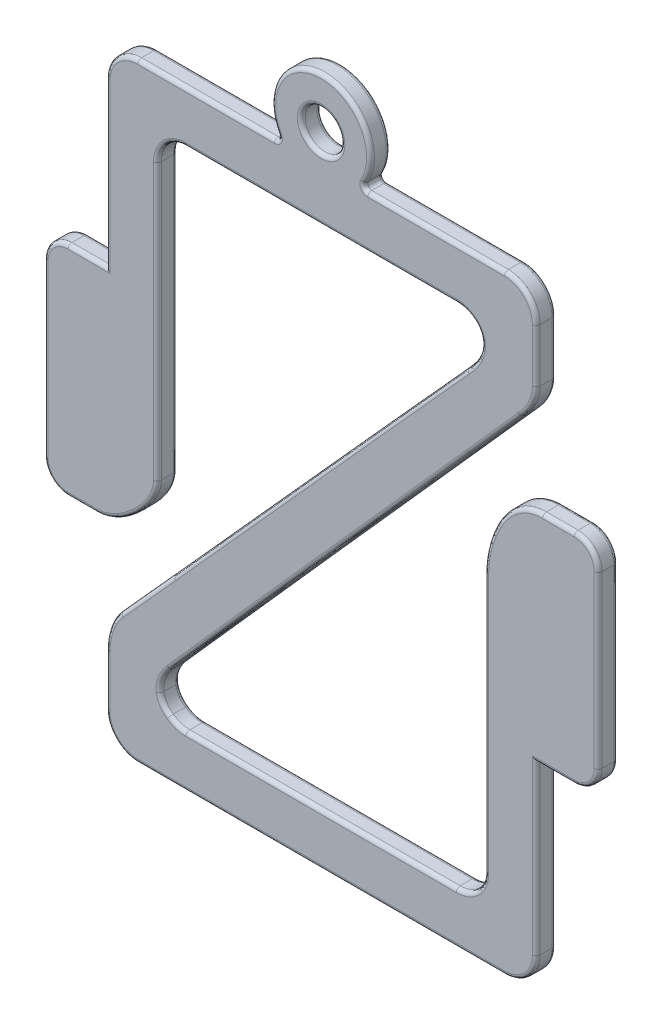
SolidWorks part; units mm, degrees
ref_plane "Front Plane" through (0, 0, 0) normal (0, 0, 1) x (1, 0, 0)
ref_plane "Top Plane" through (0, 0, 0) normal (0, 1, 0) x (1, 0, 0)
ref_plane "Right Plane" through (0, 0, 0) normal (1, 0, 0) x (0, 0, -1)
sketch "Model" plane through (0, 0, 0) normal (0, 0, 1) x (1, 0, 0)
  line L0 (214.5261, -387.7216) -> (400.0983, -387.7216)
  line L1 (416.1801, -371.6397) -> (416.1801, -286.4355)
  line L2 (416.1801, -286.4355) -> (435.3281, -286.4355)
  line L3 (447.4755, -274.288) -> (447.4755, -188.0817)
  line L4 (390.072, -215.7441) -> (390.072, -347.2106)
  line L5 (375.6692, -361.6134) -> (238.9382, -361.6134)
  line L6 (382.343, -168.4294) -> (408.5034, -139.0448)
  line L7 (416.1801, -122.3426) -> (416.1801, -95.415)
  line L8 (400.0983, -79.3331) -> (327.2017, -79.3331)
  line L9 (198.4355, -95.415) -> (198.4355, -177.9567)
  line L10 (198.4355, -177.9567) -> (179.2875, -177.9567)
  line L11 (167.1405, -190.1037) -> (167.1405, -276.2939)
  line L12 (179.2875, -288.4409) -> (194.0092, -288.4409)
  line L13 (224.5437, -259.4452) -> (224.5437, -119.8354)
  line L14 (238.9382, -105.4413) -> (375.6779, -105.4413)
  line L15 (232.264, -296.5676) -> (205.7062, -325.978)
  line L16 (198.4355, -346.519) -> (198.4355, -371.631)
  line L17 (287.4139, -79.3331) -> (214.5174, -79.3331)
  circle A0 centre (307.3078, -64.1927) radius 10
  arc A1 (327.2017, -79.3331) -> (287.4139, -79.3331) centre (307.3078, -64.1927) ccw
  spline S0 degree 3 poles (400.0983, -387.7216) (408.9799, -387.7216) (416.1801, -380.5214) (416.1801, -371.6397) knots 1 1 1 1 2 2 2 2
  spline S1 degree 3 poles (435.3281, -286.4355) (442.0368, -286.4355) (447.4755, -280.9967) (447.4755, -274.288) knots 4 4 4 4 5 5 5 5
  spline S2 degree 3 poles (447.4755, -188.0817) (447.4755, -181.3734) (442.1009, -175.935) (435.3927, -175.9342) knots 6 6 6 6 7 7 7 7
  spline S3 degree 3 poles (435.3927, -175.9342) (431.2123, -175.9334) (425.97, -175.9334) (419.396, -175.9334) knots 7 7 7 7 8 8 8 8
  spline S4 degree 3 poles (419.396, -175.9334) (398.6739, -175.9334) (390.072, -201.8602) (390.072, -215.7441) knots 8 8 8 8 9 9 9 9
  spline S5 degree 3 poles (390.072, -347.2106) (390.072, -355.165) (383.6235, -361.6134) (375.6692, -361.6134) knots 10 10 10 10 11 11 11 11
  spline S6 degree 3 poles (238.9382, -361.6134) (235.8086, -361.6134) (232.9211, -360.6794) (230.5695, -358.8986) knots 12 12 12 12 13 13 13 13
  spline S7 degree 3 poles (230.5695, -358.8986) (227.9156, -357.0488) (226.2299, -354.4207) (225.8322, -351.3946) knots 13 13 13 13 14 14 14 14
  spline S8 degree 3 poles (225.8322, -351.3946) (225.3133, -347.4871) (226.9817, -343.2164) (230.777, -338.7037) knots 14 14 14 14 15 15 15 15
  spline S9 degree 3 poles (230.777, -338.7037) (236.1196, -332.3408) (376.3782, -175.121) (382.343, -168.4294) knots 15 15 15 15 16 16 16 16
  spline S10 degree 3 poles (408.5034, -139.0448) (408.8318, -138.7077) (416.1801, -131.5495) (416.1801, -122.3426) knots 17 17 17 17 18 18 18 18
  spline S11 degree 3 poles (416.1801, -95.415) (416.1801, -86.5698) (408.9435, -79.3331) (400.0983, -79.3331) knots 19 19 19 19 20 20 20 20
  spline S12 degree 3 poles (214.5174, -79.3331) (205.6726, -79.3331) (198.4355, -86.5698) (198.4355, -95.415) knots 21 21 21 21 22 22 22 22
  spline S13 degree 3 poles (179.2875, -177.9567) (172.5789, -177.9567) (167.1405, -183.3951) (167.1405, -190.1037) knots 24 24 24 24 25 25 25 25
  spline S14 degree 3 poles (167.1405, -276.2939) (167.1405, -283.0025) (172.5789, -288.4409) (179.2875, -288.4409) knots 26 26 26 26 27 27 27 27
  spline S15 degree 3 poles (194.0092, -288.4409) (206.5622, -288.4409) (224.5437, -271.3756) (224.5437, -259.4452) knots 28 28 28 28 29 29 29 29
  spline S16 degree 3 poles (224.5437, -119.8354) (224.5437, -111.8858) (230.9885, -105.4413) (238.9382, -105.4413) knots 30 30 30 30 31 31 31 31
  spline S17 degree 3 poles (375.6779, -105.4413) (378.79, -105.4413) (381.6775, -106.3749) (384.0287, -108.1387) knots 32 32 32 32 33 33 33 33
  spline S18 degree 3 poles (384.0287, -108.1387) (386.5103, -109.8677) (388.118, -112.5821) (388.4381, -115.6942) knots 33 33 33 33 34 34 34 34
  spline S19 degree 3 poles (388.4381, -115.6942) (388.9395, -120.527) (386.4584, -125.7831) (380.856, -131.7483) knots 34 34 34 34 35 35 35 35
  spline S20 degree 3 poles (380.856, -131.7483) (372.0813, -141.1195) (233.6558, -295.0113) (232.264, -296.5676) knots 35 35 35 35 36 36 36 36
  spline S21 degree 3 poles (205.7062, -325.978) (205.1961, -326.4794) (198.4355, -333.2225) (198.4355, -346.519) knots 37 37 37 37 38 38 38 38
  spline S22 degree 3 poles (198.4355, -371.631) (198.4355, -380.481) (205.6761, -387.7216) (214.5261, -387.7216) knots 39 39 39 39 40 40 40 40
  dimension "D1" = 20
  dimension "D2" = 50
extrude "Boss-Extrude1" add sketch "Model" along normal blind 10 contours L14 S17 S18 S19 S20 L15 S21 L16 S22 L0 S0 L1 L2 S1 L3 S2 S3 S4 L4 S5 L5 S6 S7 S8 S9 L6 S10 L7 S11 L8 A1 L17 S12 L9 L10 S13 L11 S14 L12 S15 L13 S16 | A0
fillet "Fillet1" radius 2 88 edges at (317.3078, -64.1927, 0) (307.308, -105.4413, 0) (218.9851, -311.2728, 0) (198.4355, -359.075, 0) (307.3122, -387.7216, 0) (416.1801, -329.0376, 0) (425.7541, -286.4355, 0) (447.4755, -231.1848, 0) (390.072, -281.4774, 0) (307.3037, -361.6134, 0) (395.4232, -153.7371, 0) (416.1801, -108.8788, 0) (363.65, -79.3331, 0) (307.3078, -39.1927, 0) (250.9656, -79.3331, 0) (198.4355, -136.6858, 0) (188.8615, -177.9567, 0) (167.1405, -233.1988, 0) (186.6483, -288.4409, 0) (224.5437, -189.6403, 0) (317.3078, -64.1927, 10) (224.5437, -189.6403, 10) (186.6483, -288.4409, 10) (167.1405, -233.1988, 10) (188.8615, -177.9567, 10) (198.4355, -136.6858, 10) (250.9656, -79.3331, 10) (307.3078, -39.1927, 10) (363.65, -79.3331, 10) (416.1801, -108.8788, 10) (395.4232, -153.7371, 10) (307.3037, -361.6134, 10) (390.072, -281.4774, 10) (447.4755, -231.1848, 10) (425.7541, -286.4355, 10) (416.1801, -329.0376, 10) (307.3122, -387.7216, 10) (198.4355, -359.075, 10) (218.9851, -311.2728, 10) (307.308, -105.4413, 10) (287.4139, -79.3331, 5) (327.2017, -79.3331, 5)
scale "Scale1" scale about centroid uniform scaling yes scale factor 0.12
